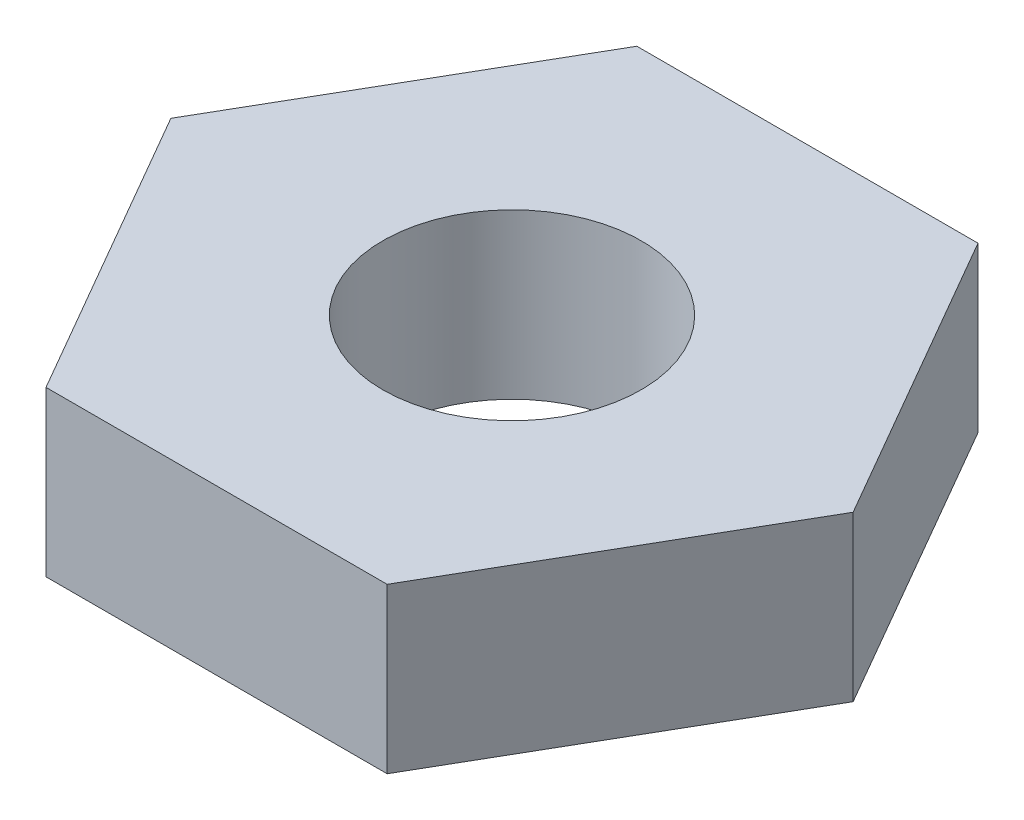
SolidWorks part; units mm, degrees
ref_plane "Front Plane" through (0, 0, 0) normal (0, 0, 1) x (1, 0, 0)
ref_plane "Top Plane" through (0, 0, 0) normal (0, 1, 0) x (1, 0, 0)
ref_plane "Right Plane" through (0, 0, 0) normal (1, 0, 0) x (0, 0, -1)
sketch "Sketch1" plane through (0, 0, 0) normal (0, 1, 0) x (1, 0, 0)
  line L1 (3.9606, 0) -> (1.9803, 3.43)
  line L2 (1.9803, 3.43) -> (-1.9803, 3.43)
  line L3 (-1.9803, 3.43) -> (-3.9606, 0)
  line L4 (-3.9606, 0) -> (-1.9803, -3.43)
  line L5 (-1.9803, -3.43) -> (1.9803, -3.43)
  line L6 (1.9803, -3.43) -> (3.9606, 0)
  circle A0 centre (0, 0) radius 3.43 construction
  circle A1 centre (0, 0) radius 1.5
  dimension "D1" = 6.86
  dimension "D2" = 3
extrude "Boss-Extrude1" add sketch "Sketch1" along normal blind 1.905 contours L5 L6 L1 L2 L3 L4 A1
